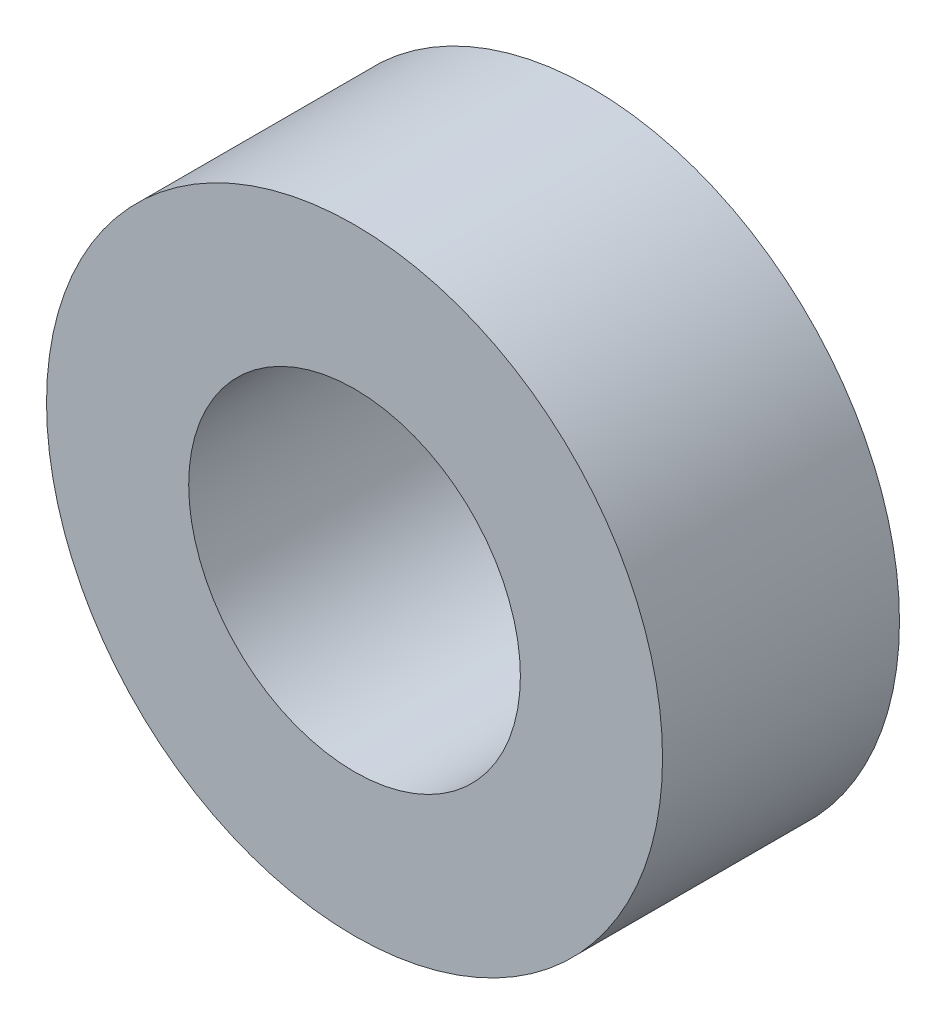
SolidWorks part; units mm, degrees
material "PE Низкой/Средней плотности"
ref_plane "Спереди" through (0, 0, 0) normal (0, 0, 1) x (1, 0, 0)
ref_plane "Сверху" through (0, 0, 0) normal (0, 1, 0) x (1, 0, 0)
ref_plane "Справа" through (0, 0, 0) normal (1, 0, 0) x (0, 0, -1)
sketch "Эскиз1" plane through (0, 0, 0) normal (0, 0, 1) x (1, 0, 0)
  circle A0 centre (0, 0) radius 6.5
  circle A1 centre (0, 0) radius 3.5
  dimension "D1" = 13
  dimension "D2" = 7
extrude "Бобышка-Вытянуть1" add sketch "Эскиз1" along normal blind 5
